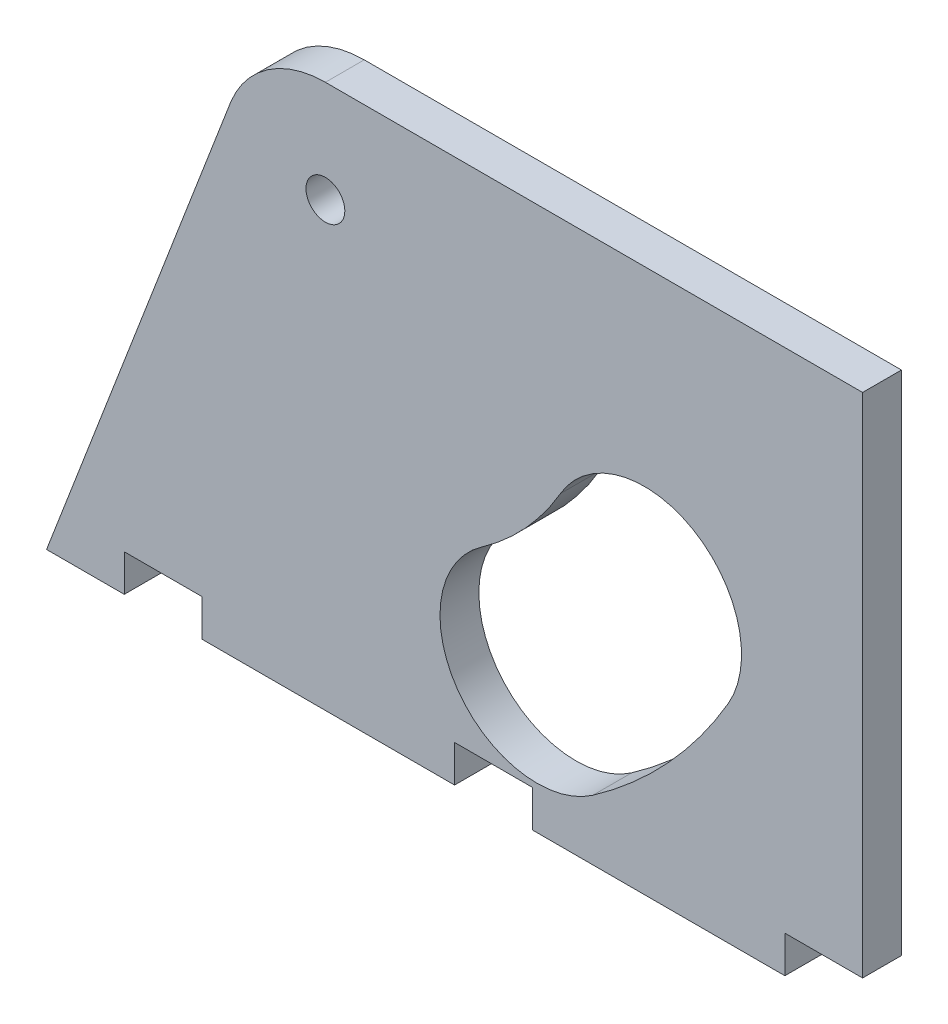
SolidWorks part; units mm, degrees
ref_plane "Front Plane" through (0, 0, 0) normal (0, 0, 1) x (1, 0, 0)
ref_plane "Top Plane" through (0, 0, 0) normal (0, 1, 0) x (1, 0, 0)
ref_plane "Right Plane" through (0, 0, 0) normal (1, 0, 0) x (0, 0, -1)
sketch "Sketch1" plane through (0, 0, 0) normal (0, 0, 1) x (1, 0, 0)
  line L1 (0, 0) -> (120, 0)
  line L2 (0, 0) -> (0, 100)
  line L3 (0, 100) -> (120, 100)
  line L4 (120, 0) -> (120, 100)
  dimension "D1" = 120
  dimension "D2" = 100
extrude "Boss-Extrude1" add sketch "Sketch1" along normal blind 5
sketch "Sketch2" plane through (0, 0, 5) normal (0, 0, 1) x (1, 0, 0)
  line L0 (0, 0) -> (120, 0) construction
  line L3 (85.2926, 7.7606) -> (120, 32.063) construction
  line L4 (120, 0) -> (120, 100) construction
  arc A0 (78.1229, 18) -> (91.9216, 33) centre (50.878, 56.9097) ccw construction
  arc A1 (85.2926, 7.7606) -> (102.7225, 26.708) centre (50.878, 56.9097) ccw
  arc A2 (70.9532, 28.2394) -> (81.1206, 39.292) centre (50.878, 56.9097) ccw
  arc A3 (70.9532, 28.2394) -> (85.2926, 7.7606) centre (78.1229, 18) ccw
  arc A4 (102.7225, 26.708) -> (81.1206, 39.292) centre (91.9216, 33) ccw
  arc A5 (50.878, 9.4097) -> (91.9216, 33) centre (50.878, 56.9097) ccw construction
  arc A6 (50.878, -25.5903) -> (122.1642, 15.3823) centre (50.878, 56.9097) ccw construction
  arc A7 (50.878, 44.4097) -> (61.6789, 50.6177) centre (50.878, 56.9097) ccw construction
  arc A8 (50.878, 44.4097) -> (50.878, -25.5903) centre (50.878, 9.4097) ccw construction
  arc A9 (122.1642, 15.3823) -> (61.6789, 50.6177) centre (91.9216, 33) ccw construction
  circle A10 centre (50.878, 56.9097) radius 2.5
  point P3 (85.8362, 24.7512)
  point P17 (74.548, 15.7274)
  point P22 (0, 0)
  point P25 (0, 0)
  point P27 (115, 5)
  dimension "D1" = 47.5
  dimension "D3" = 12.5
  dimension "D6" = 5
  dimension "D5" = 35
  dimension "D9" = 5
  dimension "D2" = 15
  dimension "D4" = 33
  dimension "D7" = 5
  dimension "D8" = 35
extrude "Cut-Extrude1" cut sketch "Sketch2" against normal through all
sketch "Sketch3" plane through (0, 0, 0) normal (0, 0, -1) x (-1, 0, 0)
  line L0 (0, 100) -> (0, 0) construction
  line L1 (-120, 0) -> (0, 0)
  line L2 (-120, 0) -> (-120, 2)
  line L3 (-120, 2) -> (0, 2)
  line L4 (0, 0) -> (0, 2)
  dimension "D1" = 2
extrude "Boss-Extrude2" add sketch "Sketch3" along normal blind 20
sketch "Sketch4" plane through (0, 0, 5) normal (0, 0, 1) x (1, 0, 0)
  line L0 (91.9216, 33) -> (50.878, 56.9097) construction
  line L1 (50.878, 56.9097) -> (78.1229, 18) construction
  line L2 (94.9418, 38.1845) -> (53.8982, 62.0942) construction
  line L3 (54.9738, 59.7776) -> (82.2186, 20.8679) construction
  line L4 (120, 0) -> (120, 100) construction
  line L5 (0, 0) -> (120, 0) construction
  arc A0 (70.2226, 38) -> (73, 50.9665) centre (64.2914, 46.0512) ccw construction
  arc A1 (71.7054, 35.9872) -> (75.1771, 52.1953) centre (64.2914, 46.0512) ccw
  arc A2 (68.7398, 40.0128) -> (70.8229, 49.7377) centre (64.2914, 46.0512) ccw
  arc A3 (68.7398, 40.0128) -> (71.7054, 35.9872) centre (70.2226, 38) ccw
  arc A4 (75.1771, 52.1953) -> (70.8229, 49.7377) centre (73, 50.9665) ccw
  point P13 (74.0696, 43.9567)
  dimension "D3" = 2.5
  dimension "D4" = 10
  dimension "D5" = 47
  dimension "D6" = 38
  dimension "D1" = 6
  dimension "D2" = 5
extrude "Cut-Extrude2" cut sketch "Sketch4" against normal through all
sketch "Sketch5" plane through (0, 0, 5) normal (0, 0, 1) x (1, 0, 0)
  line L0 (120, 70) -> (50.878, 70)
  line L1 (120, 0) -> (120, 100) construction
  line L2 (38.6579, 61.6027) -> (15, 0)
  line L3 (0, 0) -> (120, 0) construction
  line L4 (15, 0) -> (0, 0)
  line L5 (0, 0) -> (0, 100)
  line L6 (0, 100) -> (120, 100)
  line L7 (120, 100) -> (120, 70)
  arc A0 (50.878, 70) -> (38.6579, 61.6027) centre (50.878, 56.9097) ccw
  circle A1 centre (50.878, 56.9097) radius 2.5 construction
  dimension "D1" = 15
  dimension "D2" = 70
extrude "Cut-Extrude3" cut sketch "Sketch5" against normal through all
sketch "Sketch6" plane through (0, 0, 0) normal (0, 0, -1) x (-1, 0, 0)
  line L0 (-120, 2) -> (-120, 70) construction
  line L1 (-120, 30) -> (-115, 30)
  line L2 (-120, 30) -> (-120, 0)
  line L3 (-120, 0) -> (-115, 0)
  line L4 (-115, 30) -> (-115, 0)
  line L5 (-120, 0) -> (-15, 0) construction
  line L7 (-35, 0) -> (-30, 0)
  line L8 (-35, 0) -> (-35, 30)
  line L9 (-35, 30) -> (-30, 30)
  line L10 (-30, 0) -> (-30, 30)
  dimension "D1" = 5
  dimension "D2" = 30
  dimension "D3" = 5
  dimension "D4" = 30
  dimension "D5" = 80
extrude "Boss-Extrude3" add sketch "Sketch6" along normal through all
sketch "Sketch9" plane through (120, 0, 0) normal (1, 0, 0) x (0, 0, -1)
  line L0 (0, 30) -> (20, 0)
  line L1 (20, 30) -> (0, 30) construction
  line L2 (20, 0) -> (20, 30)
  line L3 (20, 30) -> (0, 30)
extrude "Cut-Extrude4" cut sketch "Sketch9" against normal through all
mirror "Mirror1" about plane through (0, 0, 5) normal (0, 0, -1) of "Cut-Extrude1", "Cut-Extrude3", "Boss-Extrude1", "Boss-Extrude2", "Boss-Extrude3", "Cut-Extrude4"
sketch "Sketch10" plane through (120, 0, 0) normal (1, 0, 0) x (0, 0, -1)
  line L0 (0, 70) -> (-10, 70) construction
  line L1 (-5, 70) -> (22.8846, 70)
  line L2 (-5, 70) -> (-5, 0)
  line L3 (-5, 0) -> (22.8846, 0)
  line L4 (22.8846, 70) -> (22.8846, 0)
  line L5 (-30, 0) -> (20, 0) construction
  dimension "D1" = 27.8846
extrude "Cut-Extrude5" cut sketch "Sketch10" against normal through all
sketch "Sketch11" plane through (120, 0, 0) normal (1, 0, 0) x (0, 0, -1)
  line L1 (-10, 30) -> (-30, 30)
  line L2 (-10, 30) -> (-10, 0)
  line L3 (-10, 0) -> (-30, 0)
  line L4 (-30, 30) -> (-30, 0)
extrude "Cut-Extrude6" cut sketch "Sketch11" against normal through all
sketch "Sketch12" plane through (0, 0, 10) normal (0, 0, 1) x (1, 0, 0)
  line L0 (15, 0) -> (120, 0) construction
  line L1 (120, 0) -> (110, 0)
  line L2 (120, 0) -> (120, 4.75)
  line L3 (120, 4.75) -> (110, 4.75)
  line L4 (110, 0) -> (110, 4.75)
  line L10 (35, 4.75) -> (110, 4.75) construction
  line L11 (67.5, 0) -> (77.5, 0)
  line L12 (67.5, 0) -> (67.5, 4.75)
  line L13 (67.5, 4.75) -> (77.5, 4.75)
  line L14 (77.5, 0) -> (77.5, 4.75)
  line L15 (25, 0) -> (35, 0)
  line L16 (25, 0) -> (25, 4.75)
  line L17 (25, 4.75) -> (35, 4.75)
  line L18 (35, 0) -> (35, 4.75)
  point P22 (72.5, 4.75)
  point P23 (72.5, 4.75)
  dimension "D1" = 4.75
  dimension "D2" = 10
  dimension "D3" = 10
  dimension "D4" = 10
  dimension "D5" = 10
extrude "Cut-Extrude7" cut sketch "Sketch12" against normal through all
